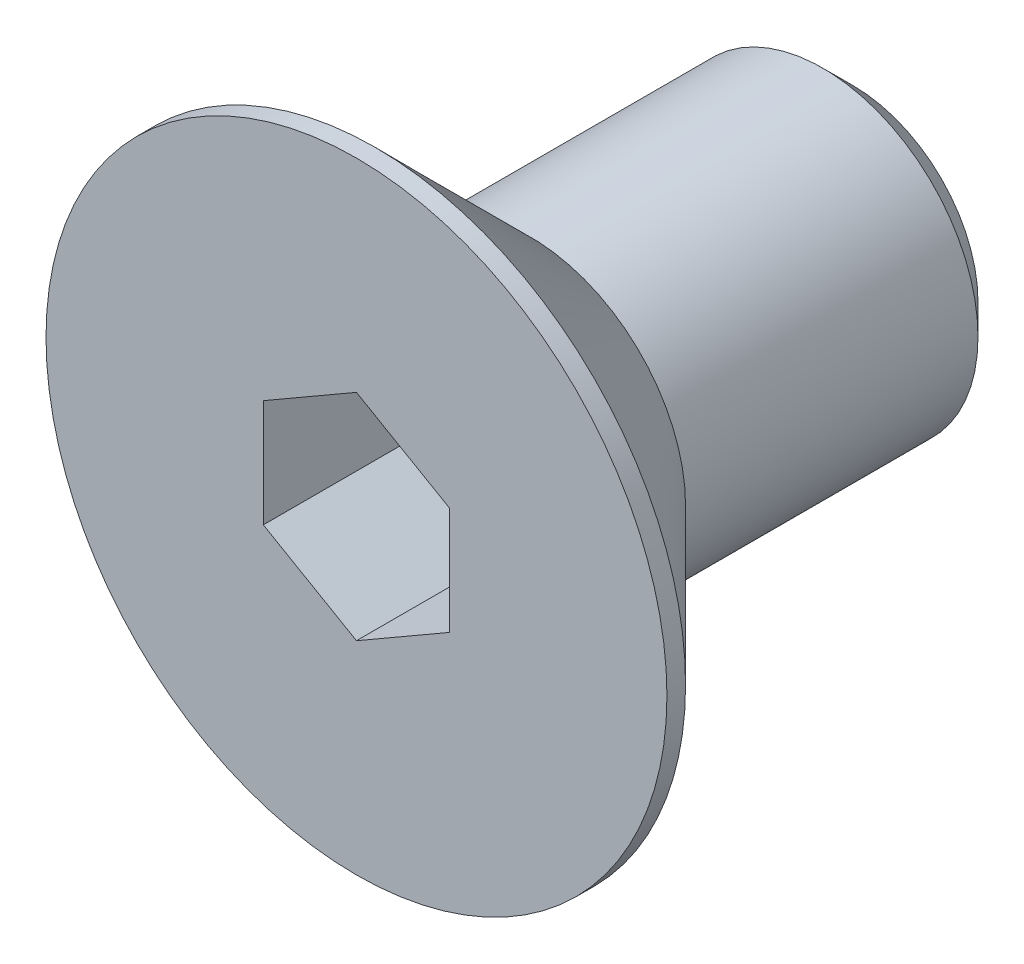
SolidWorks part; units mm, degrees
ref_plane "Piano frontale" through (0, 0, 0) normal (0, 0, 1) x (1, 0, 0)
ref_plane "Piano superiore" through (0, 0, 0) normal (0, 1, 0) x (1, 0, 0)
ref_plane "Piano destro" through (0, 0, 0) normal (1, 0, 0) x (0, 0, -1)
ref_plane "Plane1" through (0, 28.4, 0) normal (0, -1, 0) x (1, 0, 0)
sketch "Sketch1" plane through (0, 28.4, 0) normal (0, -1, 0) x (1, 0, 0)
  line L0 (-11, -2) -> (-16, -2)
  line L1 (-16, -2) -> (-16, -10)
  line L2 (-16, -10) -> (-13.5, -10)
  line L3 (-13.5, -10) -> (-13.5, -4.8)
  line L4 (-13.5, -4.8) -> (-11, -2.3)
  line L5 (-11, -2.3) -> (-11, -2)
  line L6 (-16, -2) -> (-16, -10) construction
revolve "Revolve1" add sketch "Sketch1" angle 360 about L6
sketch "Sketch2" plane through (0, 0, -2) normal (0, 0, 1) x (1, 0, 0)
  line L0 (-17.5, 29.266) -> (-17.5, 27.534)
  line L1 (-17.5, 27.534) -> (-16, 26.6679)
  line L2 (-16, 26.6679) -> (-14.5, 27.534)
  line L3 (-14.5, 27.534) -> (-14.5, 29.266)
  line L4 (-14.5, 29.266) -> (-16, 30.1321)
  line L5 (-16, 30.1321) -> (-17.5, 29.266)
extrude "Extrude1" cut sketch "Sketch2" against normal blind 2.24
sketch "Sketch3" plane through (0, 28.4, 0) normal (0, -1, 0) x (1, 0, 0)
  line L0 (-14.5, -4.24) -> (-16, -4.24)
  line L1 (-16, -4.24) -> (-16, -4.6419)
  line L2 (-16, -4.6419) -> (-14.5, -4.24)
  line L3 (-16, -4.24) -> (-16, -4.642) construction
revolve "Cut-Revolve1" cut sketch "Sketch3" angle 360 about L3
chamfer "Chamfer1" distance 0.4905 angle 45 1 edges at (-18.5, 28.4, -10)
